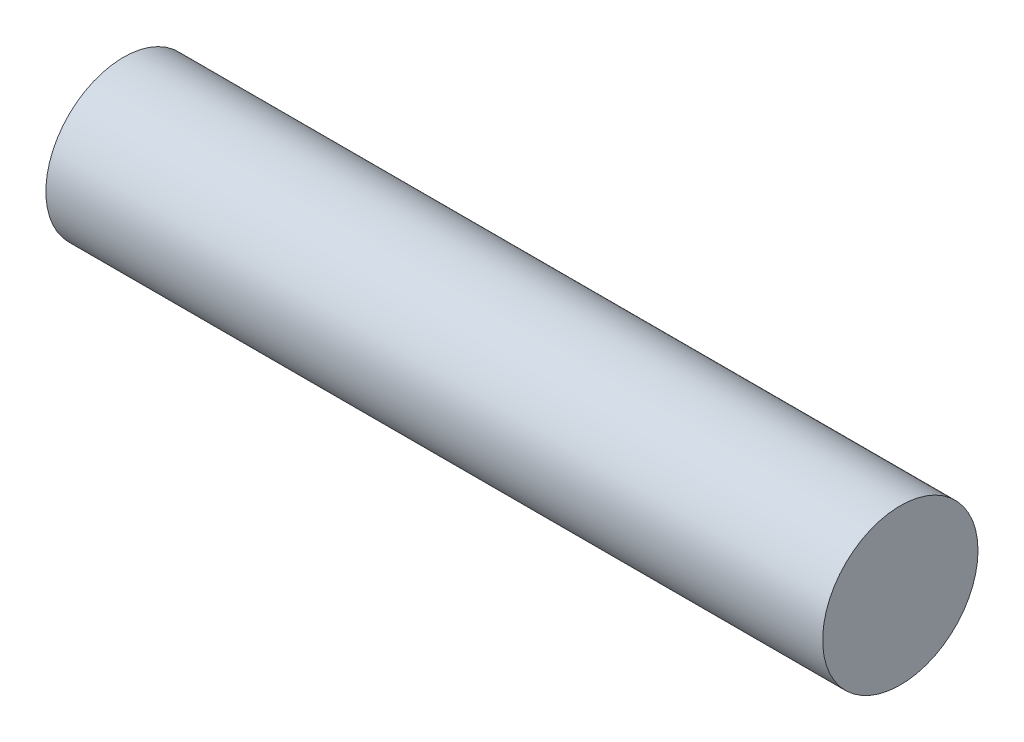
SolidWorks part; units mm, degrees
ref_plane "Front Plane" through (0, 0, 0) normal (0, 0, 1) x (1, 0, 0)
ref_plane "Top Plane" through (0, 0, 0) normal (0, 1, 0) x (1, 0, 0)
ref_plane "Right Plane" through (0, 0, 0) normal (1, 0, 0) x (0, 0, -1)
sketch "Sketch1" plane through (0, 0, 0) normal (1, 0, 0) x (0, 0, -1)
  circle A0 centre (0, 0) radius 1
  dimension "D1" = 2
extrude "Boss-Extrude1" add sketch "Sketch1" along normal blind 10
